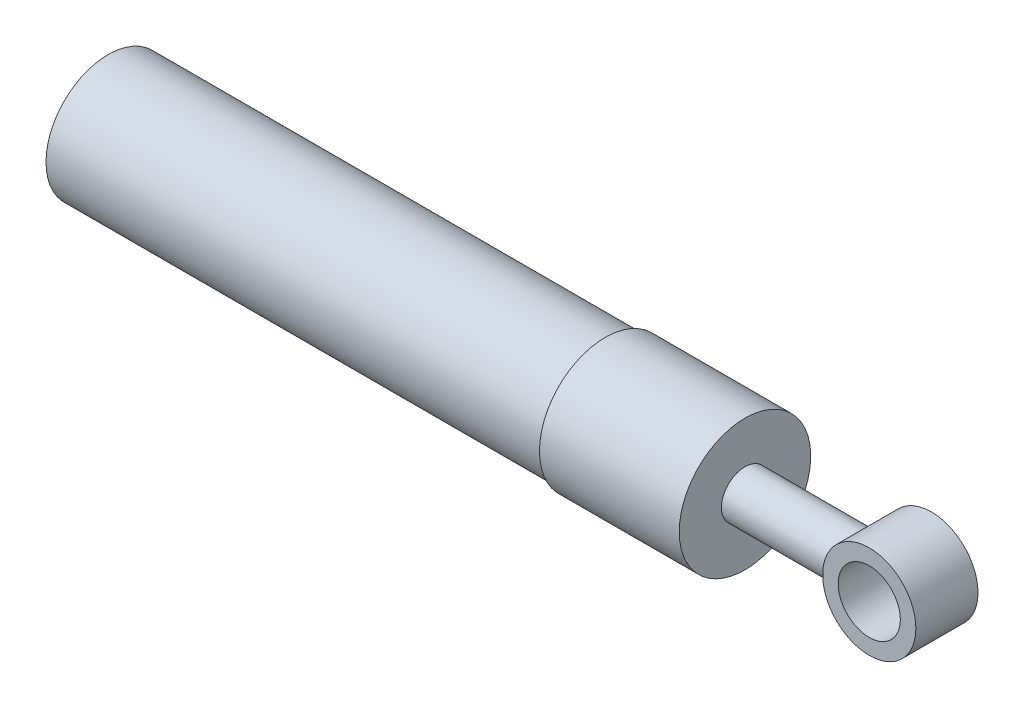
SolidWorks part; units mm, degrees
ref_plane "Front Plane" through (0, 0, 0) normal (0, 0, 1) x (1, 0, 0)
ref_plane "Top Plane" through (0, 0, 0) normal (0, 1, 0) x (1, 0, 0)
ref_plane "Right Plane" through (0, 0, 0) normal (1, 0, 0) x (0, 0, -1)
sketch "Sketch2" plane through (0, 0, 0) normal (0, 0, 1) x (1, 0, 0)
  line L0 (0, 0) -> (0, 6.35)
  line L1 (0, 6.35) -> (50.8, 6.35)
  line L2 (50.8, 6.35) -> (50.8, 6.7183)
  line L3 (50.8, 6.7183) -> (65.0875, 6.7183)
  line L4 (65.0875, 6.7183) -> (65.0875, 2.413)
  line L5 (65.0875, 2.413) -> (77.7875, 2.413)
  line L6 (77.7875, 2.413) -> (77.7875, 0)
  line L7 (0, 0) -> (77.7875, 0)
  dimension "D1" = 6.35
  dimension "D2" = 50.8
  dimension "D3" = 14.2875
  dimension "D4" = 12.7
  dimension "D5" = 6.7183
  dimension "D6" = 2.413
revolve "Revolve1" add sketch "Sketch2" angle 360 about L7
sketch "Sketch3" plane through (0, 0, 0) normal (0, 0, 1) x (1, 0, 0)
  line L0 (77.7875, -2.413) -> (77.7875, 2.413) construction
  circle A0 centre (80.9625, 0) radius 3.175
  circle A1 centre (80.9625, 0) radius 4.7625
  dimension "D1" = 1.5875
  dimension "D2" = 6.35
extrude "Boss-Extrude1" add sketch "Sketch3" along normal mid plane 6.35
